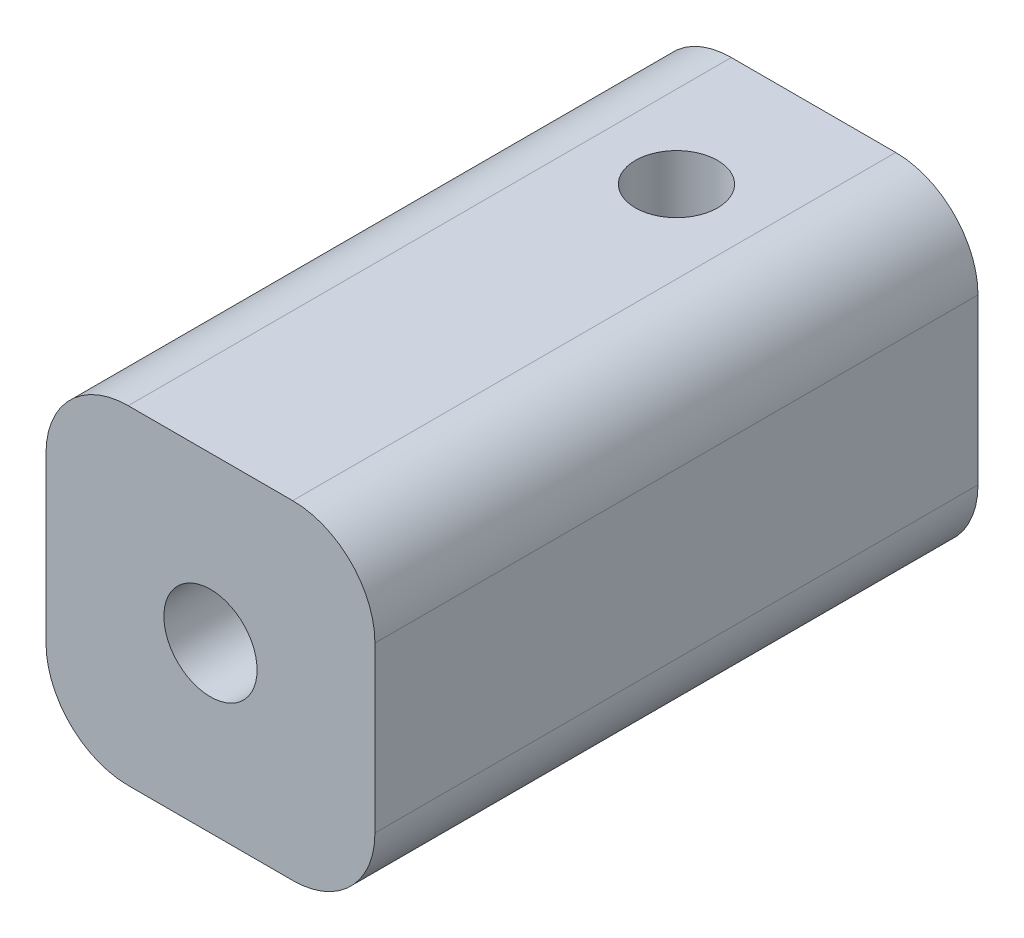
SolidWorks part; units mm, degrees
ref_plane "Plano frontal" through (0, 0, 0) normal (0, 0, 1) x (1, 0, 0)
ref_plane "Plano superior" through (0, 0, 0) normal (0, 1, 0) x (1, 0, 0)
ref_plane "Plano direito" through (0, 0, 0) normal (1, 0, 0) x (0, 0, -1)
sketch "Esboço1" plane through (0, 0, 0) normal (0, 0, 1) x (1, 0, 0)
  line L0 (7.4717, 5.2075) -> (19.4717, -6.7925) construction
  line L1 (7.4717, 5.2075) -> (19.4717, 5.2075)
  line L2 (7.4717, 5.2075) -> (7.4717, -6.7925)
  line L3 (7.4717, -6.7925) -> (19.4717, -6.7925)
  line L4 (19.4717, 5.2075) -> (19.4717, -6.7925)
  line L5 (19.4717, 5.2075) -> (7.4717, -6.7925) construction
  circle A0 centre (13.4717, -0.7925) radius 1.7
  dimension "D3" = 3.4
  dimension "D1" = 12
  dimension "D2" = 12
extrude "Ressalto-extrusão1" add sketch "Esboço1" along normal blind 22
sketch "Esboço2" plane through (0, 0, 0) normal (0, 1, 0) x (1, 0, 0)
  line L0 (13.4717, 0) -> (13.4717, -22) construction
  line L1 (19.4717, 0) -> (7.4717, 0) construction
  line L2 (19.4717, -22) -> (7.4717, -22) construction
  line L3 (7.4717, -5) -> (19.4717, -5) construction
  line L4 (7.4717, -22) -> (7.4717, 0) construction
  line L5 (19.4717, -22) -> (19.4717, 0) construction
  circle A0 centre (13.4717, -5) radius 1.5
  dimension "D2" = 3
  dimension "D1" = 5
extrude "Corte-extrusão1" cut sketch "Esboço2" along normal blind 7 and the other way blind 10
fillet "Filete2" radius 3 1 edges at (7.4717, 5.2075, 11)
fillet "Filete3" radius 3 1 edges at (7.4717, -6.7925, 11)
fillet "Filete4" radius 3 1 edges at (19.4717, -6.7925, 11)
fillet "Filete5" radius 3 1 edges at (19.4717, 5.2075, 11)
